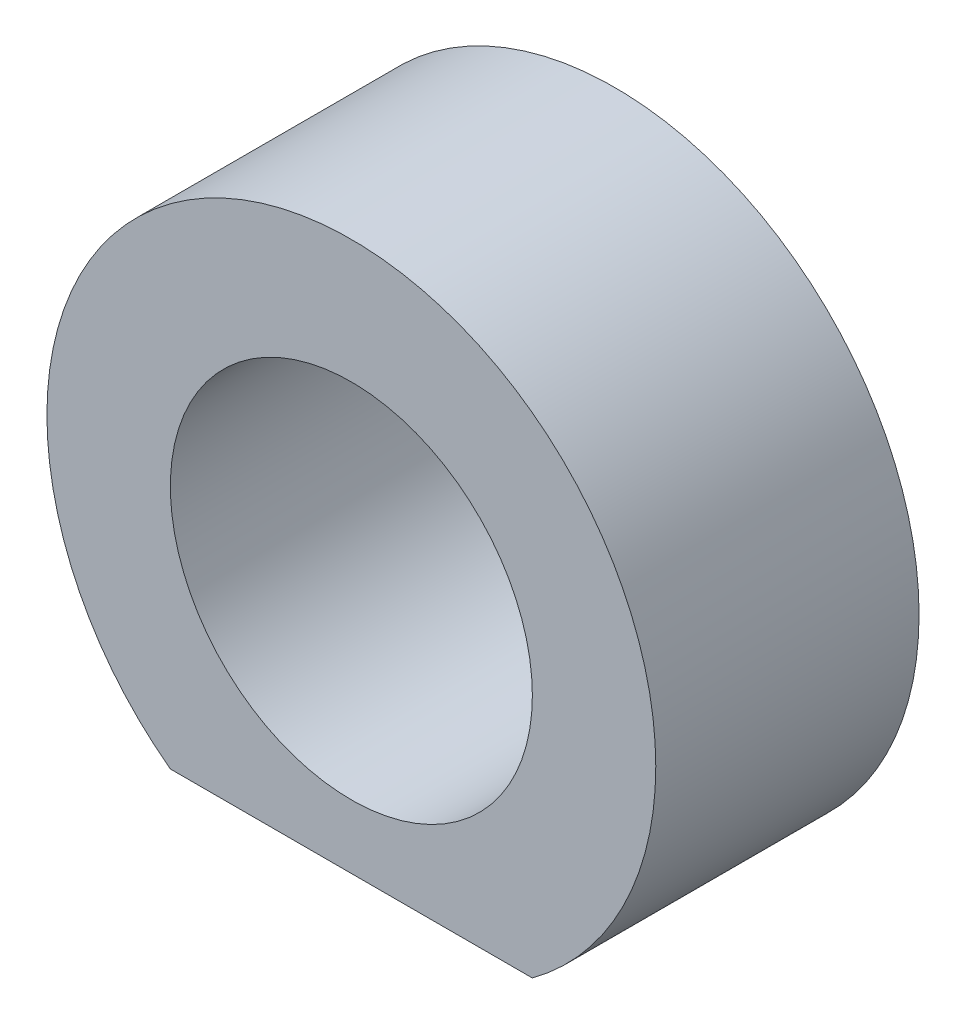
SolidWorks part; units mm, degrees
ref_plane "Front Plane" through (0, 0, 0) normal (0, 0, 1) x (1, 0, 0)
ref_plane "Top Plane" through (0, 0, 0) normal (0, 1, 0) x (1, 0, 0)
ref_plane "Right Plane" through (0, 0, 0) normal (1, 0, 0) x (0, 0, -1)
sketch "Sketch1" plane through (0, 0, 0) normal (0, 0, 1) x (1, 0, 0)
  circle A0 centre (0, 0) radius 18.5
  circle A1 centre (0, 0) radius 11
  dimension "D1" = 37
  dimension "D2" = 22
extrude "Boss-Extrude1" add sketch "Sketch1" along normal mid plane 16
sketch "Sketch3" plane through (0, 0, -8) normal (0, 0, -1) x (-1, 0, 0)
  line L0 (-11, -14.8745) -> (11, -14.8745)
  circle A0 centre (0, 0) radius 18.5 construction
  arc A1 (-11, -14.8745) -> (11, -14.8745) centre (0, 0) ccw
  dimension "D1" = 22
extrude "Cut-Extrude1" cut sketch "Sketch3" against normal blind 16
sketch "Sketch4" plane through (0, -14.8745, 0) normal (0, -1, 0) x (1, 0, 0)
  circle A0 centre (0, 0) radius 1
  point P0 (0, 0)
extrude "Cut-Extrude2" cut sketch "Sketch4" against normal blind 2
chamfer "Chamfer1" distance 0.3 angle 45 1 edges at (0, -12.8745, -1)
